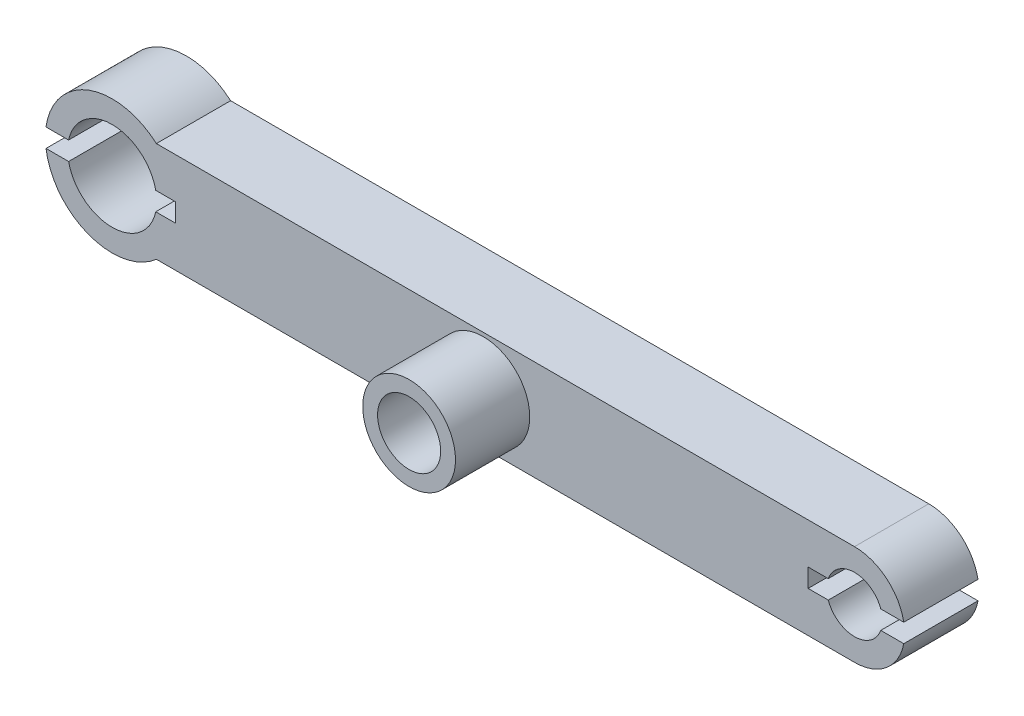
SolidWorks part; units mm, degrees
material "ABS"
ref_plane "Plan de face" through (0, 0, 0) normal (0, 0, 1) x (1, 0, 0)
ref_plane "Plan de dessus" through (0, 0, 0) normal (0, 1, 0) x (1, 0, 0)
ref_plane "Plan de droite" through (0, 0, 0) normal (1, 0, 0) x (0, 0, -1)
sketch "Esquisse1" plane through (0, 0, 0) normal (0, 0, 1) x (1, 0, 0)
  circle A0 centre (0, 0) radius 2.4
  circle A1 centre (0, 0) radius 3.6
  dimension "D1" = 4.8
  dimension "D2" = 1.2
extrude "CC_AXE_SERVO" add sketch "Esquisse1" along normal blind 3.9
sketch "Esquisse3" plane through (0, 0, 0) normal (0, 0, 1) x (1, 0, 0)
  line L0 (0, 0) -> (40, 0) construction
  circle A0 centre (40, 0) radius 1.5
  circle A1 centre (40, 0) radius 2.7
  dimension "D1" = 3
  dimension "D2" = 1.2
  dimension "D3" = 40
extrude "CC_PIVOT_JAMBE" add sketch "Esquisse3" along normal blind 3.9 separate body
sketch "Esquisse4" plane through (0, 0, 0) normal (0, 0, 1) x (1, 0, 0)
  line L0 (0, 0) -> (40, 0) construction
  line L1 (2.3812, 2.7) -> (40, 2.7)
  line L2 (2.3812, -2.7) -> (40, -2.7)
  circle A1 centre (0, 0) radius 3.6 construction
  arc A3 (2.3812, 2.7) -> (2.3812, -2.7) centre (0, 0) ccw
  circle A4 centre (0, 0) radius 2.4 construction
  circle A5 centre (0, 0) radius 2.4
  circle A6 centre (40, 0) radius 1.5 construction
  circle A7 centre (40, 0) radius 1.5
  circle A8 centre (40, 0) radius 2.7 construction
  arc A9 (40, -2.7) -> (40, 2.7) centre (40, 0) ccw
extrude "LIAISON" add sketch "Esquisse4" along normal blind 4
sketch "Esquisse9" plane through (0, 0, 0) normal (0, 0, 1) x (1, 0, 0)
  line L0 (0, 0) -> (3.4, 0) construction
  line L1 (3.4, 0.5) -> (-3.6, 0.5)
  line L2 (3.4, 0.5) -> (3.4, -0.5)
  line L3 (3.4, -0.5) -> (-3.6, -0.5)
  line L4 (-3.6, 0.5) -> (-3.6, -0.5)
  arc A1 (2.3812, 2.7) -> (2.3812, -2.7) centre (0, 0) ccw construction
  circle A2 centre (0, 0) radius 2.4 construction
  point P11 (2.4, 0)
  dimension "D1" = 1
  dimension "D2" = 1
extrude "ELASTICITE_AXE_SERVO" cut sketch "Esquisse9" along normal through all
sketch "Esquisse7" plane through (0, 0, 0) normal (0, 0, 1) x (1, 0, 0)
  line L0 (0, 0) -> (20, 0) construction
  circle A0 centre (20, 0) radius 1.7
  dimension "D1" = 3.4
  dimension "D2" = 20
extrude "PASSAGE_VIS" cut sketch "Esquisse7" along normal through all
sketch "Esquisse8" plane through (0, 0, 4) normal (0, 0, 1) x (1, 0, 0)
  circle A1 centre (20, 0) radius 1.7 construction
  circle A2 centre (20, 0) radius 2.5
  circle A3 centre (20, 0) radius 1.7
  dimension "D1" = 0.8
extrude "BUTEE_ASSEMBLAGE" add sketch "Esquisse8" along normal blind 4
sketch "Esquisse10" plane through (0, 0, 0) normal (0, 0, 1) x (1, 0, 0)
  line L0 (40, 0) -> (37.5, 0) construction
  line L1 (37.5, -0.5) -> (42.7, -0.5)
  line L2 (37.5, -0.5) -> (37.5, 0.5)
  line L3 (37.5, 0.5) -> (42.7, 0.5)
  line L4 (42.7, -0.5) -> (42.7, 0.5)
  circle A0 centre (40, 0) radius 1.5 construction
  circle A1 centre (40, 0) radius 1.5 construction
  arc A2 (40, -2.7) -> (40, 2.7) centre (40, 0) ccw construction
  circle A3 centre (40, 0) radius 1.5 construction
  point P11 (38.5, 0)
  dimension "D1" = 1
  dimension "D2" = 1
extrude "ELASTICITE" cut sketch "Esquisse10" along normal through all
